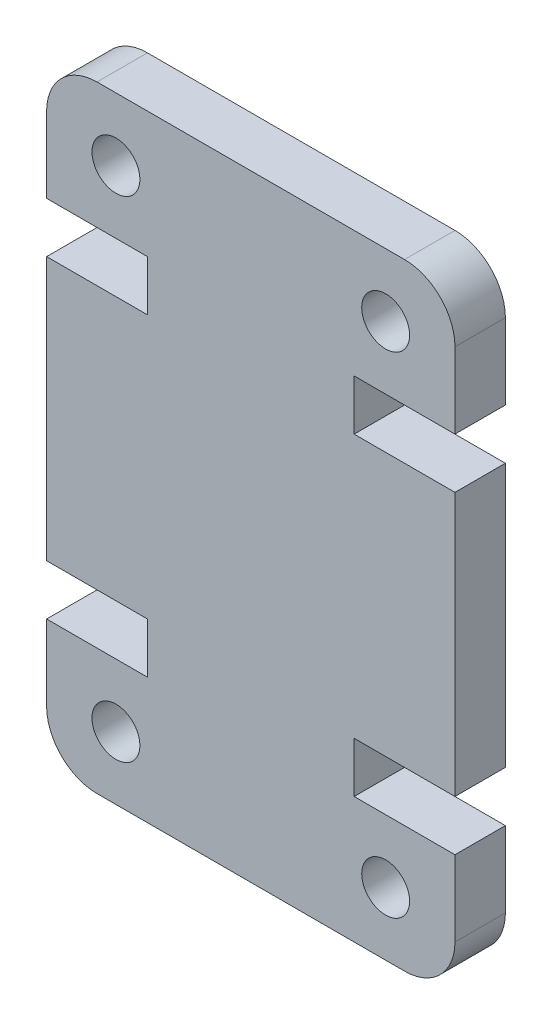
SolidWorks part; units mm, degrees
ref_plane "Front Plane" through (0, 0, 0) normal (0, 0, 1) x (1, 0, 0)
ref_plane "Top Plane" through (0, 0, 0) normal (0, 1, 0) x (1, 0, 0)
ref_plane "Right Plane" through (0, 0, 0) normal (1, 0, 0) x (0, 0, -1)
sketch "Sketch1" plane through (0, 0, 0) normal (0, 0, 1) x (1, 0, 0)
  line L0 (0, 17.45) -> (0, 7)
  line L1 (16.2, 5) -> (16.2, 2)
  line L2 (12.2, 5) -> (16.2, 5)
  line L3 (2, 0) -> (14.2, 0)
  line L4 (16.2, 7) -> (12.2, 7)
  line L5 (12.2, 7) -> (12.2, 5)
  line L6 (16.2, 17.45) -> (16.2, 7)
  line L7 (0, 19.45) -> (0, 22.45)
  line L8 (4, 19.45) -> (0, 19.45)
  line L9 (0, 17.45) -> (4, 17.45)
  line L10 (4, 7) -> (4, 5)
  line L11 (4, 17.45) -> (4, 19.45)
  line L12 (0, 7) -> (4, 7)
  line L13 (4, 5) -> (0, 5)
  line L14 (12.2, 17.45) -> (12.2, 19.45)
  line L15 (16.2, 17.45) -> (12.2, 17.45)
  line L16 (2, 24.45) -> (14.2, 24.45)
  line L17 (12.2, 19.45) -> (16.2, 19.45)
  line L18 (16.2, 19.45) -> (16.2, 22.45)
  line L19 (0, 5) -> (0, 2)
  line L20 (0, 12.225) -> (16.2, 12.225) construction
  line L21 (8.1, 24.45) -> (8.1, 0) construction
  circle A0 centre (13.45, 2.5) radius 0.95
  arc A1 (16.2, 2) -> (14.2, 0) centre (14.2, 2) cw
  circle A2 centre (2.75, 21.95) radius 0.95
  arc A3 (0, 2) -> (2, 0) centre (2, 2) ccw
  arc A4 (0, 22.45) -> (2, 24.45) centre (2, 22.45) cw
  circle A5 centre (2.75, 2.5) radius 0.95
  arc A6 (16.2, 22.45) -> (14.2, 24.45) centre (14.2, 22.45) ccw
  circle A7 centre (13.45, 21.95) radius 0.95
  point P17 (8.1, 12.225)
  dimension "D1" = 1.9
  dimension "D2" = 2
  dimension "D3" = 2.75
  dimension "D4" = 8.1
  dimension "D5" = 2.5
  dimension "D6" = 5
  dimension "D8" = 12.225
extrude "Boss-Extrude1" add sketch "Sketch1" along normal blind 4
sketch "Sketch2" plane through (0, 0, 0) normal (0, 0, -1) x (-1, 0, 0)
  line L0 (0, 0) -> (0, 24.45)
  line L1 (0, 24.45) -> (-16.2, 24.45)
  line L2 (-16.2, 24.45) -> (-16.2, 0)
  line L3 (-16.2, 0) -> (0, 0)
extrude "Cut-Extrude1" cut sketch "Sketch2" against normal blind 2
